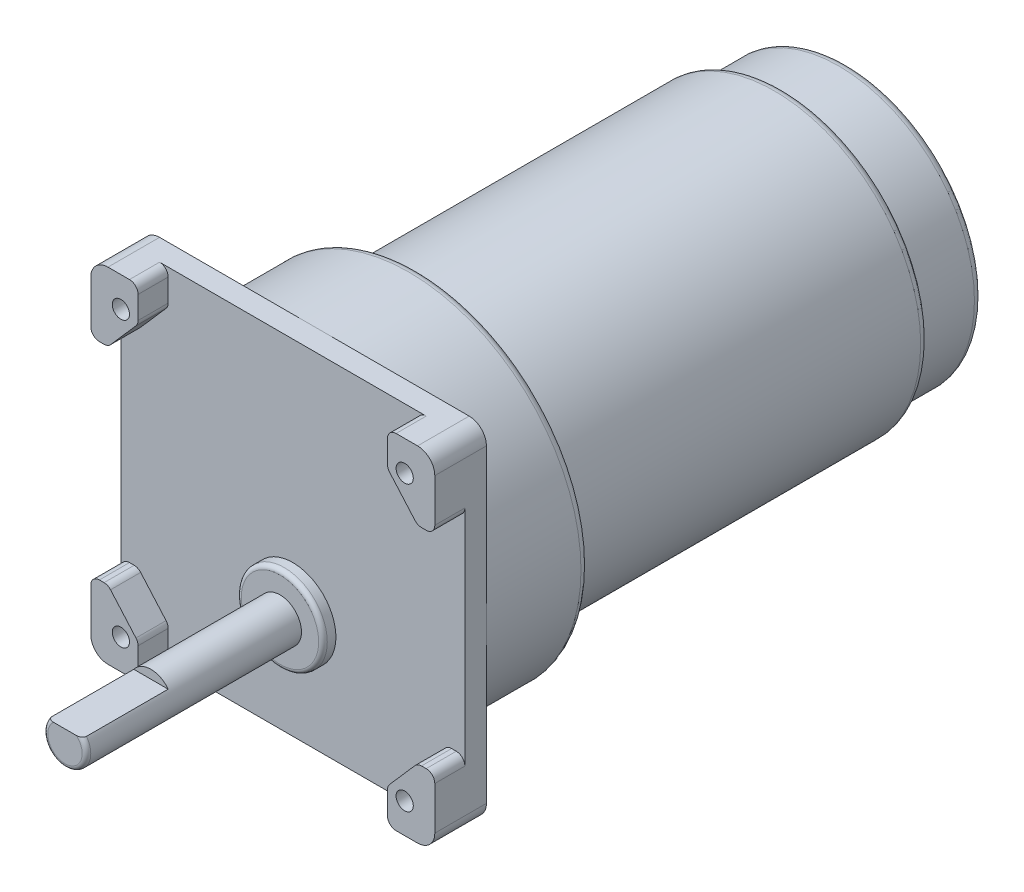
SolidWorks part; units mm, degrees
ref_plane "Front Plane" through (0, 0, 0) normal (0, 0, 1) x (1, 0, 0)
ref_plane "Top Plane" through (0, 0, 0) normal (0, 1, 0) x (1, 0, 0)
ref_plane "Right Plane" through (0, 0, 0) normal (1, 0, 0) x (0, 0, -1)
sketch "Sketch1" plane through (0, 0, 0) normal (0, 0, 1) x (1, 0, 0)
  circle A0 centre (0, 0) radius 40
  dimension "D1" = 80
extrude "Boss-Extrude1" add sketch "Sketch1" along normal blind 24
sketch "Sketch2" plane through (0, 0, 24) normal (0, 0, 1) x (1, 0, 0)
  line L0 (0, 0) -> (13.9236, 0) construction
  line L1 (-40, -40) -> (40, -40)
  line L2 (-40, -40) -> (-40, 40)
  line L3 (-40, 40) -> (40, 40)
  line L4 (40, -40) -> (40, 40)
  line L5 (-40, -40) -> (40, 40) construction
  line L6 (-40, 40) -> (40, -40) construction
  circle A0 centre (0, 0) radius 40 construction
  circle A1 centre (33, -33) radius 2
  circle A2 centre (-33, 33) radius 2
  circle A3 centre (33, 33) radius 2
  circle A4 centre (-33, -33) radius 2
  point P0 (0, 0)
  dimension "D1" = 4
  dimension "D2" = 66
extrude "Boss-Extrude2" add sketch "Sketch2" along normal blind 5
fillet "Fillet1" radius 4 4 edges at (-40, 40, 26.5) (40, 40, 26.5) (40, -40, 26.5) (-40, -40, 26.5)
sketch "Sketch3" plane through (0, 0, 0) normal (0, 0, -1) x (-1, 0, 0)
  circle A0 centre (0, 0) radius 34
  dimension "D1" = 68
extrude "Boss-Extrude3" add sketch "Sketch3" along normal blind 100
sketch "Sketch4" plane through (0, 0, 29) normal (0, 0, 1) x (1, 0, 0)
  line L1 (0, -15) -> (0, -33) construction
  line L2 (0, -33) -> (-33, -33) construction
  line L3 (0, -33) -> (33, -33) construction
  circle A0 centre (0, -15) radius 10
  point P0 (0, 0)
  point P4 (0, -15)
  point P9 (0, -5)
  dimension "D1" = 15
  dimension "D2" = 20
extrude "Boss-Extrude4" add sketch "Sketch4" along normal blind 3
sketch "Sketch5" plane through (0, 0, 32) normal (0, 0, 1) x (1, 0, 0)
  circle A0 centre (0, -15) radius 5
  point P3 (0, 0)
  dimension "D1" = 10
extrude "Boss-Extrude5" add sketch "Sketch5" along normal blind 50
fillet "Fillet3" radius 1 1 edges at (10, -15, 32)
fillet "Fillet4" radius 1 1 edges at (5, -15, 82)
sketch "Sketch6" plane through (-40, 0, 0) normal (-1, 0, 0) x (0, 0, 1)
  line L0 (81, -10) -> (32, -10) construction
  line L1 (62, -10) -> (88.9791, -10)
  line L2 (62, -10) -> (62, -12)
  line L3 (62, -12) -> (88.9791, -12)
  line L4 (88.9791, -10) -> (88.9791, -12)
  line L5 (82, -19) -> (82, -11) construction
  dimension "D1" = 2
  dimension "D2" = 20
extrude "Cut-Extrude1" cut sketch "Sketch6" against normal through all both and the other way through all
sketch "Sketch8" plane through (0, 0, 29) normal (0, 0, 1) x (1, 0, 0)
  line L0 (-40, 24) -> (-36, 24)
  line L1 (-40, 36) -> (-40, -36) construction
  line L2 (-36, 24) -> (-29, 32)
  line L3 (-29, 32) -> (-29, 40)
  line L4 (36, 40) -> (-36, 40) construction
  line L5 (0, -7.7134) -> (0, 18.0911) construction
  line L6 (-8.3596, 0) -> (10.225, 0) construction
  line L7 (-40, 36) -> (-40, 24)
  line L8 (-29, 40) -> (-36, 40)
  line L9 (29, 40) -> (36, 40)
  line L10 (40, 36) -> (40, 24)
  line L11 (29, 32) -> (29, 40)
  line L12 (36, 24) -> (29, 32)
  line L13 (40, 24) -> (36, 24)
  line L14 (40, -24) -> (36, -24)
  line L15 (36, -24) -> (29, -32)
  line L16 (29, -32) -> (29, -40)
  line L17 (40, -36) -> (40, -24)
  line L18 (29, -40) -> (36, -40)
  line L19 (-29, -40) -> (-36, -40)
  line L20 (-40, -36) -> (-40, -24)
  line L21 (-29, -32) -> (-29, -40)
  line L22 (-36, -24) -> (-29, -32)
  line L23 (-40, -24) -> (-36, -24)
  arc A0 (-36, 40) -> (-40, 36) centre (-36, 36) ccw construction
  arc A1 (-36, 40) -> (-40, 36) centre (-36, 36) ccw
  arc A2 (36, 40) -> (40, 36) centre (36, 36) cw
  arc A3 (36, -40) -> (40, -36) centre (36, -36) ccw
  arc A4 (-36, -40) -> (-40, -36) centre (-36, -36) cw
  line M6 (36, 40) -> (-36, 40)
  arc M7 (-36, 40) -> (-40, 36) centre (-36, 36) ccw
  line M8 (-40, 36) -> (-40, -36)
  arc M9 (-40, -36) -> (-36, -40) centre (-36, -36) ccw
  line M10 (-36, -40) -> (36, -40)
  arc M11 (36, -40) -> (40, -36) centre (36, -36) ccw
  line M12 (40, -36) -> (40, 36)
  arc M13 (40, 36) -> (36, 40) centre (36, 36) ccw
  circle M14 centre (33, -33) radius 2
  circle M15 centre (-33, 33) radius 2
  circle M16 centre (33, 33) radius 2
  circle M17 centre (-33, -33) radius 2
  dimension "D1" = 16
  dimension "D2" = 11
  dimension "D3" = 4
  dimension "D4" = 8
extrude "Boss-Extrude6" add sketch "Sketch8" along normal blind 7 contours L23 L21 L22 M8 M9 M10 M17 | L15 L16 L14 M10 M11 M12 M14 | L2 L3 L0 M6 M7 M8 M15 | L13 L11 L12 M12 M13 M6 M16
fillet "Fillet5" radius 2 16 edges at (36, -24, 32.5) (29, -32, 32.5) (-36, -24, 32.5) (-29, -32, 32.5) (29, 32, 32.5) (36, 24, 32.5) (-29, 32, 32.5) (-36, 24, 32.5) (29, 40, 32.5) (40, 24, 32.5) (-29, 40, 32.5) (-40, 24, 32.5) (-29, -40, 32.5) (29, -40, 32.5) (40, -24, 32.5) (-40, -24, 32.5)
sketch "Sketch10" plane through (0, 0, -100) normal (0, 0, -1) x (-1, 0, 0)
  circle A0 centre (0, 0) radius 31.5
  circle A2 centre (0, 0) radius 34
  circle A3 centre (0, 0) radius 34
  dimension "D2" = 63
  dimension "D1" = 0
extrude "Cut-Extrude3" cut sketch "Sketch10" against normal blind 15
fillet "Fillet6" radius 2 1 edges at (-31.5, 0, -100)
fillet "Fillet7" radius 2 1 edges at (-34, 0, -85)
fillet "Fillet8" radius 2 1 edges at (40, 0, 0)
